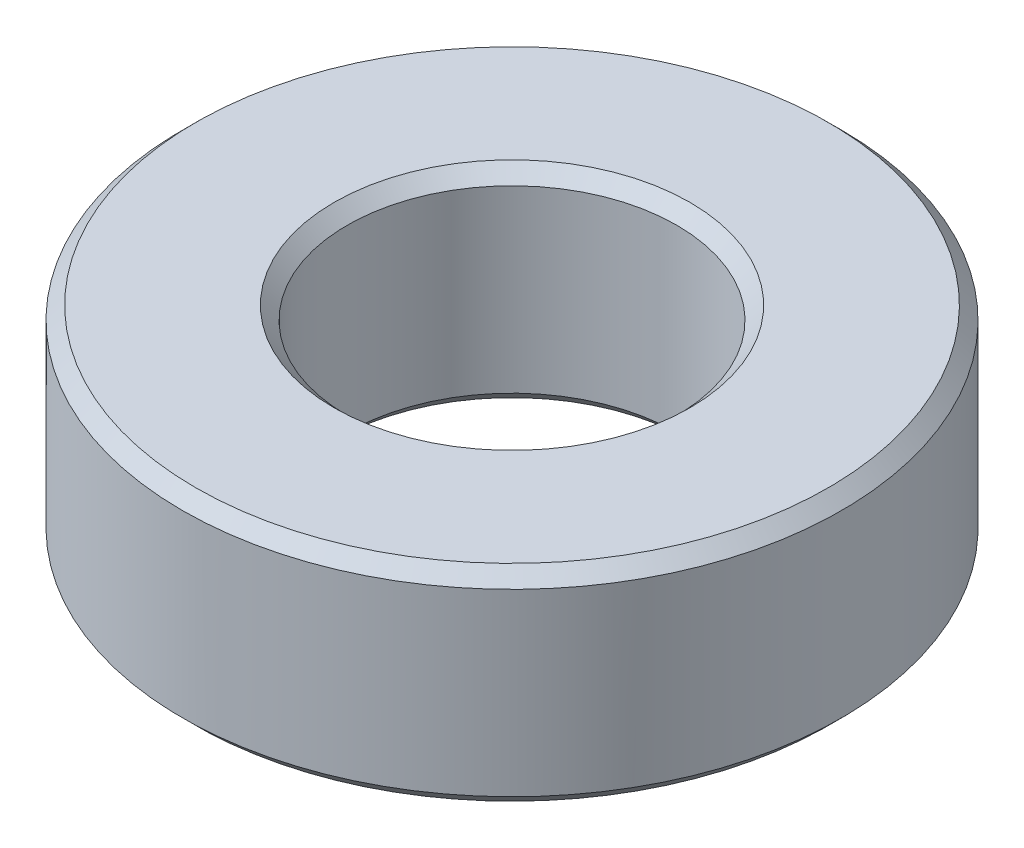
SolidWorks part; units mm, degrees
ref_plane "Front Plane" through (0, 0, 0) normal (0, 0, 1) x (1, 0, 0)
ref_plane "Top Plane" through (0, 0, 0) normal (0, 1, 0) x (1, 0, 0)
ref_plane "Right Plane" through (0, 0, 0) normal (1, 0, 0) x (0, 0, -1)
sketch "Sketch1" plane through (0, 0, 0) normal (0, 0, 1) x (1, 0, 0)
  line L0 (0, -0.6526) -> (0, 0.6526) construction
  line L1 (3.175, 1.9844) -> (3.175, -1.9844)
  line L2 (3.175, -1.9844) -> (6.35, -1.9844)
  line L3 (6.35, -1.9844) -> (6.35, 1.9844)
  line L4 (6.35, 1.9844) -> (3.175, 1.9844)
  point P7 (3.175, 0)
  dimension "D1" = 3.9688
  dimension "D2" = 12.7
  dimension "D3" = 6.35
revolve "Revolve1" add sketch "Sketch1" angle 360 about L0
chamfer "Chamfer1" distance 0.254 angle 45 4 edges at (0, -1.9844, -6.35) (0, 1.9844, -6.35) (0, 1.9844, -3.175) (0, -1.9844, -3.175)
